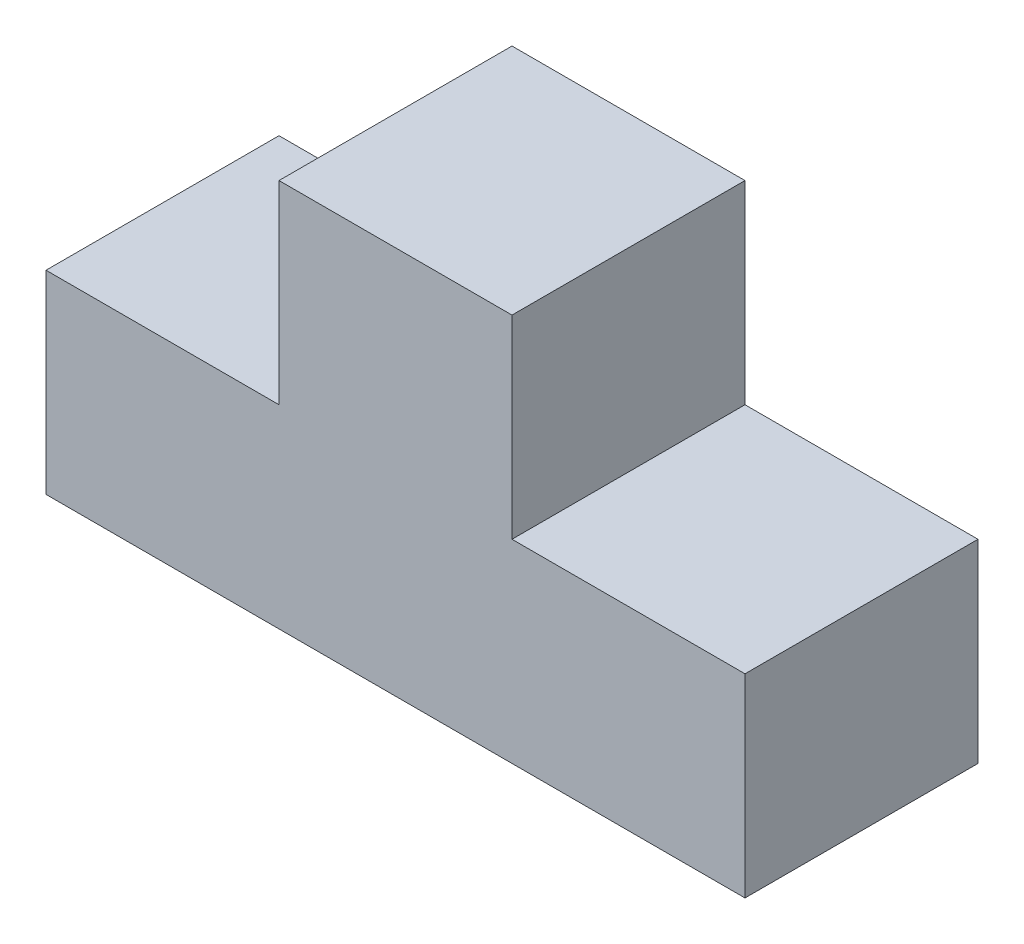
SolidWorks part; units mm, degrees
ref_plane "Front Plane" through (0, 0, 0) normal (0, 0, 1) x (1, 0, 0)
ref_plane "Top Plane" through (0, 0, 0) normal (0, 1, 0) x (1, 0, 0)
ref_plane "Right Plane" through (0, 0, 0) normal (1, 0, 0) x (0, 0, -1)
sketch "Sketch1" plane through (0, 0, 0) normal (0, 0, 1) x (1, 0, 0)
  line L0 (-45, 0) -> (45, 0)
  line L1 (45, 0) -> (45, 25)
  line L2 (45, 25) -> (15, 25)
  line L3 (15, 25) -> (15, 50)
  line L4 (15, 50) -> (-15, 50)
  line L5 (0, 50) -> (0, 0) construction
  line L6 (-15, 25) -> (-15, 50)
  line L7 (-45, 25) -> (-15, 25)
  line L8 (-45, 0) -> (-45, 25)
  dimension "D1" = 90
  dimension "D2" = 50
  dimension "D3" = 25
  dimension "D4" = 30
extrude "Boss-Extrude1" add sketch "Sketch1" along normal blind 30
